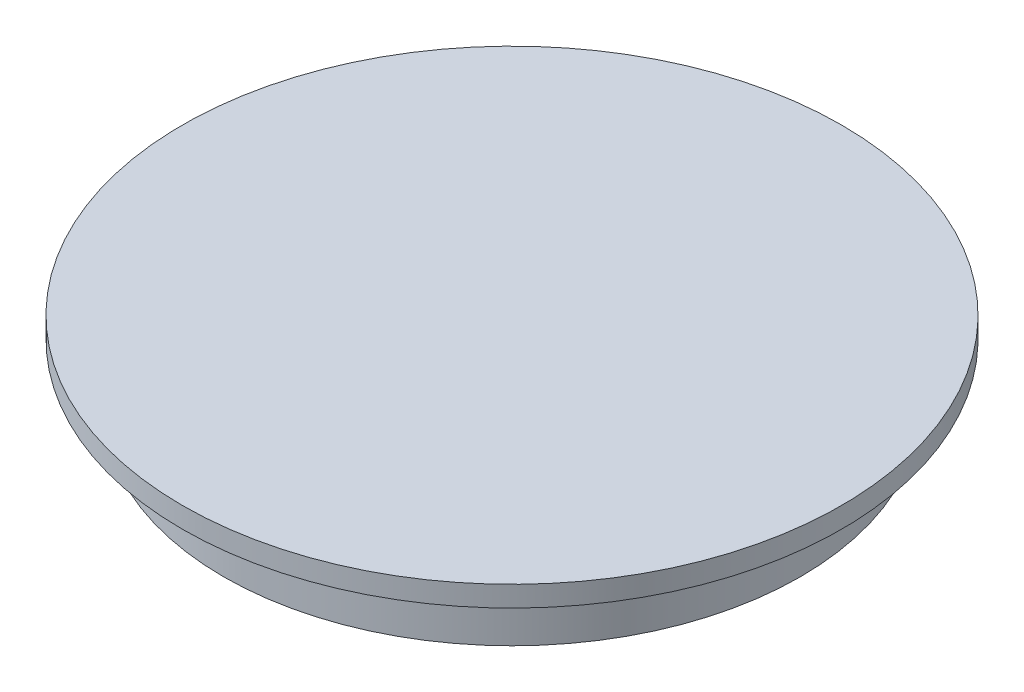
SolidWorks part; units mm, degrees
ref_plane "Front Plane" through (0, 0, 0) normal (0, 0, 1) x (1, 0, 0)
ref_plane "Top Plane" through (0, 0, 0) normal (0, 1, 0) x (1, 0, 0)
ref_plane "Right Plane" through (0, 0, 0) normal (1, 0, 0) x (0, 0, -1)
sketch "Sketch1" plane through (0, 0, 0) normal (0, 0, 1) x (1, 0, 0)
  line L0 (0, 0) -> (-50.8, 0)
  line L1 (-50.8, 0) -> (-50.8, -3.175)
  line L2 (-50.8, -3.175) -> (-44.45, -3.175)
  line L3 (-44.45, -3.175) -> (-44.45, -12.7)
  line L4 (-44.45, -12.7) -> (0, -12.7)
  line L5 (0, -12.7) -> (0, 0)
  dimension "D1" = 50.8
  dimension "D2" = 44.45
  dimension "D3" = 3.175
  dimension "D4" = 9.525
revolve "Revolve1" add sketch "Sketch1" angle 360 about L5
sketch "Sketch2" plane through (0, -12.7, 0) normal (0, -1, 0) x (1, 0, 0)
  circle A0 centre (0, 0) radius 41.275
  circle A1 centre (0, 0) radius 44.45 construction
  dimension "D1" = 3.175
extrude "Cut-Extrude1" cut sketch "Sketch2" against normal up to surface (9.525 mm away) up to face at (0, -3.175, -44.45)
